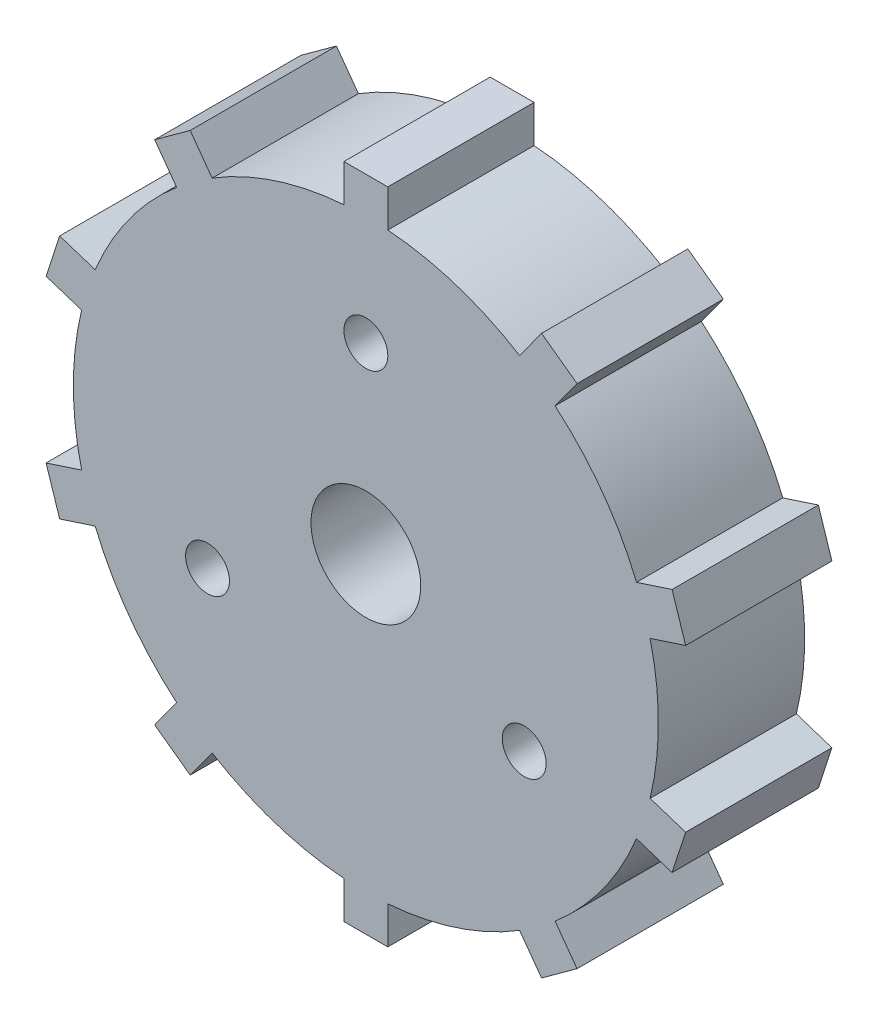
SolidWorks part; units mm, degrees
ref_plane "前视基准面" through (0, 0, 0) normal (0, 0, 1) x (1, 0, 0)
ref_plane "上视基准面" through (0, 0, 0) normal (0, 1, 0) x (1, 0, 0)
ref_plane "右视基准面" through (0, 0, 0) normal (1, 0, 0) x (0, 0, -1)
sketch "草图1" plane through (0, 0, 0) normal (0, 0, 1) x (1, 0, 0)
  line L1 (1.5, 19.9437) -> (1.5, 22.5)
  line L2 (-1.5, 19.9437) -> (-1.5, 22.5)
  line L3 (-1.5, 22.5) -> (1.5, 22.5)
  line L4 (10.5091, 17.0164) -> (12.0116, 19.0846)
  line L5 (12.0116, 19.0846) -> (14.4387, 17.3212)
  line L6 (12.9361, 15.2531) -> (14.4387, 17.3212)
  line L7 (18.504, 7.5895) -> (20.9352, 8.3795)
  line L8 (20.9352, 8.3795) -> (21.8623, 5.5263)
  line L9 (19.4311, 4.7363) -> (21.8623, 5.5263)
  line L10 (19.4311, -4.7363) -> (21.8623, -5.5263)
  line L11 (21.8623, -5.5263) -> (20.9352, -8.3795)
  line L12 (18.504, -7.5895) -> (20.9352, -8.3795)
  line L13 (12.9361, -15.2531) -> (14.4387, -17.3212)
  line L14 (14.4387, -17.3212) -> (12.0116, -19.0846)
  line L15 (10.5091, -17.0164) -> (12.0116, -19.0846)
  line L16 (1.5, -19.9437) -> (1.5, -22.5)
  line L17 (1.5, -22.5) -> (-1.5, -22.5)
  line L18 (-1.5, -19.9437) -> (-1.5, -22.5)
  line L19 (-10.5091, -17.0164) -> (-12.0116, -19.0846)
  line L20 (-12.0116, -19.0846) -> (-14.4387, -17.3212)
  line L21 (-12.9361, -15.2531) -> (-14.4387, -17.3212)
  line L22 (-18.504, -7.5895) -> (-20.9352, -8.3795)
  line L23 (-20.9352, -8.3795) -> (-21.8623, -5.5263)
  line L24 (-19.4311, -4.7363) -> (-21.8623, -5.5263)
  line L25 (-19.4311, 4.7363) -> (-21.8623, 5.5263)
  line L26 (-21.8623, 5.5263) -> (-20.9352, 8.3795)
  line L27 (-18.504, 7.5895) -> (-20.9352, 8.3795)
  line L28 (-12.9361, 15.2531) -> (-14.4387, 17.3212)
  line L29 (-14.4387, 17.3212) -> (-12.0116, 19.0846)
  line L30 (-10.5091, 17.0164) -> (-12.0116, 19.0846)
  arc A0 (-1.5, 19.9437) -> (-10.5091, 17.0164) centre (0, 0) ccw
  circle A1 centre (0, 12.5) radius 1.5
  circle A2 centre (10.8253, -6.25) radius 1.5
  circle A3 centre (-10.8253, -6.25) radius 1.5
  arc A4 (-19.4311, 4.7363) -> (-19.4311, -4.7363) centre (0, 0) ccw
  arc A5 (-12.9361, 15.2531) -> (-18.504, 7.5895) centre (0, 0) ccw
  arc A6 (10.5091, 17.0164) -> (1.5, 19.9437) centre (0, 0) ccw
  arc A7 (18.504, 7.5895) -> (12.9361, 15.2531) centre (0, 0) ccw
  arc A8 (19.4311, -4.7363) -> (19.4311, 4.7363) centre (0, 0) ccw
  arc A9 (12.9361, -15.2531) -> (18.504, -7.5895) centre (0, 0) ccw
  arc A10 (1.5, -19.9437) -> (10.5091, -17.0164) centre (0, 0) ccw
  arc A11 (-10.5091, -17.0164) -> (-1.5, -19.9437) centre (0, 0) ccw
  arc A12 (-18.504, -7.5895) -> (-12.9361, -15.2531) centre (0, 0) ccw
  point P47 (0, 0)
  point P51 (0, 0)
  dimension "D1" = 40
  dimension "D2" = 10
  dimension "D5" = 12.5
  dimension "D3" = 3
extrude "凸台-拉伸1" add sketch "草图1" along normal blind 10
sketch "草图2" plane through (0, 0, 0) normal (0, 0, 1) x (1, 0, 0)
  circle A0 centre (0, 0) radius 3.75
  dimension "D1" = 7.5
extrude "切除-拉伸1" cut sketch "草图2" along normal blind 10
